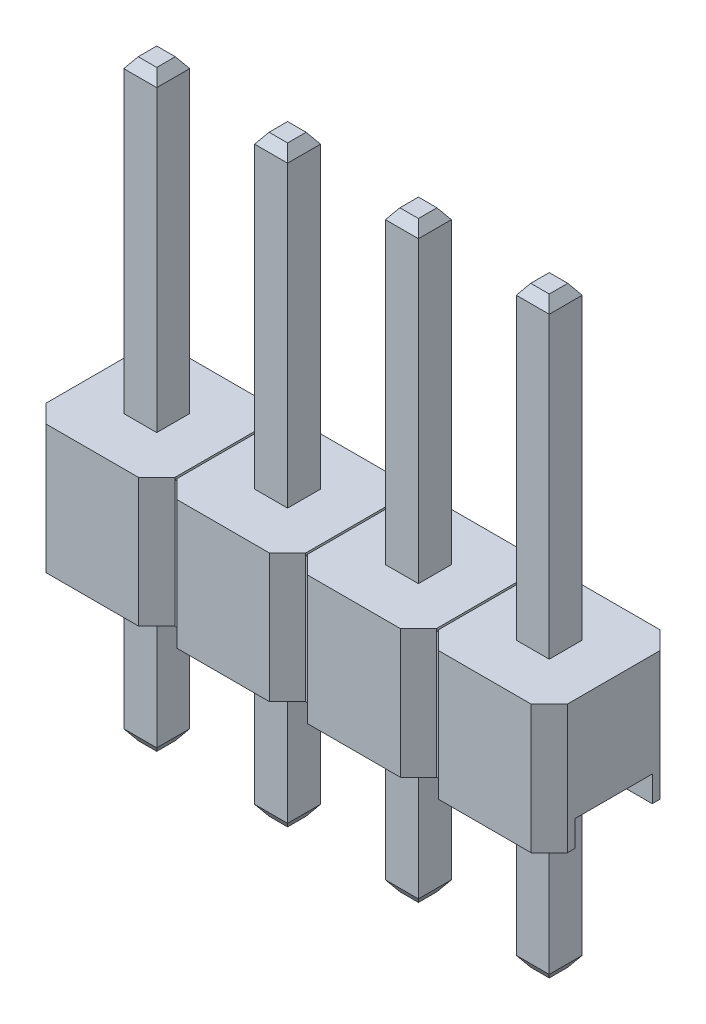
SolidWorks part; units mm, degrees
ref_plane "Front Plane" through (0, 0, 0) normal (0, 0, 1) x (1, 0, 0)
ref_plane "Top Plane" through (0, 0, 0) normal (0, 1, 0) x (1, 0, 0)
ref_plane "Right Plane" through (0, 0, 0) normal (1, 0, 0) x (0, 0, -1)
sketch "Sketch1" plane through (0, 0, 0) normal (0, 1, 0) x (1, 0, 0)
  line L0 (0, 2.15) -> (0.35, 2.5)
  line L1 (0.35, 0) -> (2.15, 0)
  line L2 (0, 0.35) -> (0, 2.15)
  line L3 (0.35, 2.5) -> (2.15, 2.5)
  line L5 (2.15, 2.5) -> (2.5, 2.15)
  line L6 (0, 0.35) -> (0.35, 0)
  line L7 (2.15, 0) -> (2.5, 0.35)
  line L9 (2.54, 0.35) -> (2.89, 0)
  line L10 (2.54, 2.15) -> (2.89, 2.5)
  line L11 (2.89, 0) -> (4.69, 0)
  line L12 (4.69, 0) -> (5.04, 0.35)
  line L14 (4.69, 2.5) -> (5.04, 2.15)
  line L15 (2.89, 2.5) -> (4.69, 2.5)
  line L17 (5.08, 0.35) -> (5.43, 0)
  line L18 (5.08, 2.15) -> (5.43, 2.5)
  line L19 (5.43, 0) -> (7.23, 0)
  line L20 (7.23, 0) -> (7.58, 0.35)
  line L22 (7.23, 2.5) -> (7.58, 2.15)
  line L23 (5.43, 2.5) -> (7.23, 2.5)
  line L25 (7.62, 0.35) -> (7.97, 0)
  line L26 (7.62, 2.15) -> (7.97, 2.5)
  line L27 (7.97, 0) -> (9.77, 0)
  line L28 (9.77, 0) -> (10.12, 0.35)
  line L30 (9.77, 2.5) -> (10.12, 2.15)
  line L31 (7.97, 2.5) -> (9.77, 2.5)
  line L64 (0, 0.35) -> (2.54, 0.35) construction
  line L65 (2.5, 2.15) -> (2.54, 2.15)
  line L67 (5.04, 2.15) -> (5.08, 2.15)
  line L68 (2.54, 0.35) -> (2.54, 2.15) [skipped]
  line L69 (5.08, 0.35) -> (5.08, 2.15) [skipped]
  line L70 (7.58, 2.15) -> (7.62, 2.15)
  line L71 (7.62, 0.35) -> (7.62, 2.15) [skipped]
  line L73 (10.16, 0.35) -> (10.16, 2.15) [skipped]
  line L75 (12.7, 0.35) -> (12.7, 2.15) [skipped]
  line L76 (15.24, 0.35) -> (15.24, 2.15) [skipped]
  line L77 (17.78, 0.35) -> (17.78, 2.15) [skipped]
  line L82 (7.62, 0.35) -> (7.58, 0.35)
  line L83 (5.08, 0.35) -> (5.04, 0.35)
  line L84 (2.54, 0.35) -> (2.5, 0.35)
  line L86 (10.16, 2.15) -> (10.51, 2.5) [skipped]
  line L87 (10.16, 0.35) -> (10.51, 0) [skipped]
  line L88 (10.51, 2.5) -> (12.31, 2.5) [skipped]
  line L89 (12.31, 2.5) -> (12.66, 2.15) [skipped]
  line L90 (12.7, 2.15) -> (13.05, 2.5) [skipped]
  line L91 (13.05, 2.5) -> (14.85, 2.5) [skipped]
  line L92 (15.24, 2.15) -> (15.59, 2.5) [skipped]
  line L93 (17.39, 2.5) -> (17.74, 2.15) [skipped]
  line L94 (17.78, 2.15) -> (18.13, 2.5) [skipped]
  line L95 (19.93, 2.5) -> (20.28, 2.15) [skipped]
  line L96 (15.59, 2.5) -> (17.39, 2.5) [skipped]
  line L97 (18.13, 2.5) -> (19.93, 2.5) [skipped]
  line L98 (18.13, 0) -> (19.93, 0) [skipped]
  line L99 (15.59, 0) -> (17.39, 0) [skipped]
  line L100 (14.85, 2.5) -> (15.2, 2.15) [skipped]
  line L101 (13.05, 0) -> (14.85, 0) [skipped]
  line L102 (12.31, 0) -> (12.66, 0.35) [skipped]
  line L103 (10.51, 0) -> (12.31, 0) [skipped]
  line L104 (12.7, 0.35) -> (13.05, 0) [skipped]
  line L105 (14.85, 0) -> (15.2, 0.35) [skipped]
  line L106 (15.24, 0.35) -> (15.59, 0) [skipped]
  line L107 (17.39, 0) -> (17.74, 0.35) [skipped]
  line L108 (17.78, 0.35) -> (18.13, 0) [skipped]
  line L109 (19.93, 0) -> (20.28, 0.35) [skipped]
  line L110 (10.12, 2.15) -> (10.12, 0.35)
  point P0 (0, 0)
  point P1 (2.5, 2.5)
  point P2 (0, 2.5)
  point P3 (2.5, 0)
  dimension "D2" = 2.5
  dimension "D3" = 2.5
  dimension "D4" = 2.54
  dimension "D5" = 8
extrude "Boss-Extrude1" add sketch "Sketch1" along normal blind 2.5
sketch "Sketch2" plane through (0, 0, 0) normal (0, -1, 0) x (1, 0, 0)
  line L0 (0, -1.25) -> (10.12, -1.25) construction
  line L3 (0, -2.15) -> (0, -0.35) construction
  line L8 (10.12, -0.35) -> (10.12, -2.15) construction
  line L10 (0, -2) -> (10.12, -2)
  line L11 (0, -2) -> (0, -0.5)
  line L12 (0, -0.5) -> (10.12, -0.5)
  line L13 (10.12, -2) -> (10.12, -0.5)
  line L14 (0, -2) -> (10.12, -0.5) construction
  line L15 (0, -0.5) -> (10.12, -2) construction
  point P6 (5.06, -1.25)
  dimension "D1" = 1.5
extrude "Cut-Extrude1" cut sketch "Sketch2" against normal blind 0.5
sketch "Sketch4" plane through (0, 2.5, 0) normal (0, 1, 0) x (1, 0, 0)
  line L0 (5.08, 2.15) -> (5.08, 0.35)
  line L1 (2.5, 2.15) -> (2.54, 2.15)
  line L2 (2.5, 2.15) -> (2.5, 0.35)
  line L3 (2.5, 0.35) -> (2.54, 0.35)
  line L4 (2.54, 2.15) -> (2.54, 0.35)
  line L5 (5.04, 2.15) -> (5.04, 0.35)
  line L6 (5.04, 2.15) -> (5.08, 2.15)
  line L7 (5.04, 0.35) -> (5.08, 0.35)
  line L8 (7.62, 2.15) -> (7.62, 0.35)
  line L9 (7.58, 2.15) -> (7.58, 0.35)
  line L10 (7.58, 2.15) -> (7.62, 2.15)
  line L11 (7.58, 0.35) -> (7.62, 0.35)
  line L12 (10.16, 2.15) -> (10.16, 0.35)
  line L13 (10.12, 2.15) -> (10.12, 0.35)
  line L14 (10.12, 2.15) -> (10.16, 2.15)
  line L15 (10.12, 0.35) -> (10.16, 0.35)
  line L16 (12.7, 2.15) -> (12.7, 0.35)
  line L17 (12.66, 2.15) -> (12.66, 0.35)
  line L18 (12.66, 2.15) -> (12.7, 2.15)
  line L19 (12.66, 0.35) -> (12.7, 0.35)
  line L20 (15.24, 2.15) -> (15.24, 0.35)
  line L21 (15.2, 2.15) -> (15.2, 0.35)
  line L22 (15.2, 2.15) -> (15.24, 2.15)
  line L23 (15.2, 0.35) -> (15.24, 0.35)
  line L24 (17.78, 2.15) -> (17.78, 0.35)
  line L25 (17.74, 2.15) -> (17.74, 0.35)
  line L26 (17.74, 2.15) -> (17.78, 2.15)
  line L27 (17.74, 0.35) -> (17.78, 0.35)
  line L28 (2.54, 2.15) -> (5.08, 2.15) construction
  dimension "D1" = 2.54
extrude "Cut-Extrude2" cut sketch "Sketch4" against normal blind 0.04
sketch "Sketch3" plane through (0, 2.5, 0) normal (0, 1, 0) x (1, 0, 0)
  line L0 (1.25, 2.5) -> (1.25, 0) construction
  line L1 (2.15, 2.5) -> (0.35, 2.5) construction
  line L2 (0.35, 0) -> (2.15, 0) construction
  line L3 (0, 1.25) -> (1.25, 1.25) construction
  line L4 (0, 2.15) -> (0, 0.35) construction
  line L6 (0.93, 0.93) -> (1.57, 0.93)
  line L7 (0.93, 0.93) -> (0.93, 1.57)
  line L8 (0.93, 1.57) -> (1.57, 1.57)
  line L9 (1.57, 0.93) -> (1.57, 1.57)
  line L10 (0.93, 0.93) -> (1.57, 1.57) construction
  line L11 (0.93, 1.57) -> (1.57, 0.93) construction
  dimension "D1" = 0.64
extrude "Boss-Extrude2" add sketch "Sketch3" along normal blind 6 and the other way blind 5.5
chamfer "Chamfer1" distance 0.2 angle 35 8 edges at (1.25, -3, -1.57) (0.93, -3, -1.25) (1.25, -3, -0.93) (1.57, -3, -1.25) (1.25, 8.5, -0.93) (0.93, 8.5, -1.25) (1.25, 8.5, -1.57) (1.57, 8.5, -1.25)
pattern_linear "LPattern1" count 4 spacing 2.54 along (1, 0, 0) of "Chamfer1", "Boss-Extrude2"
